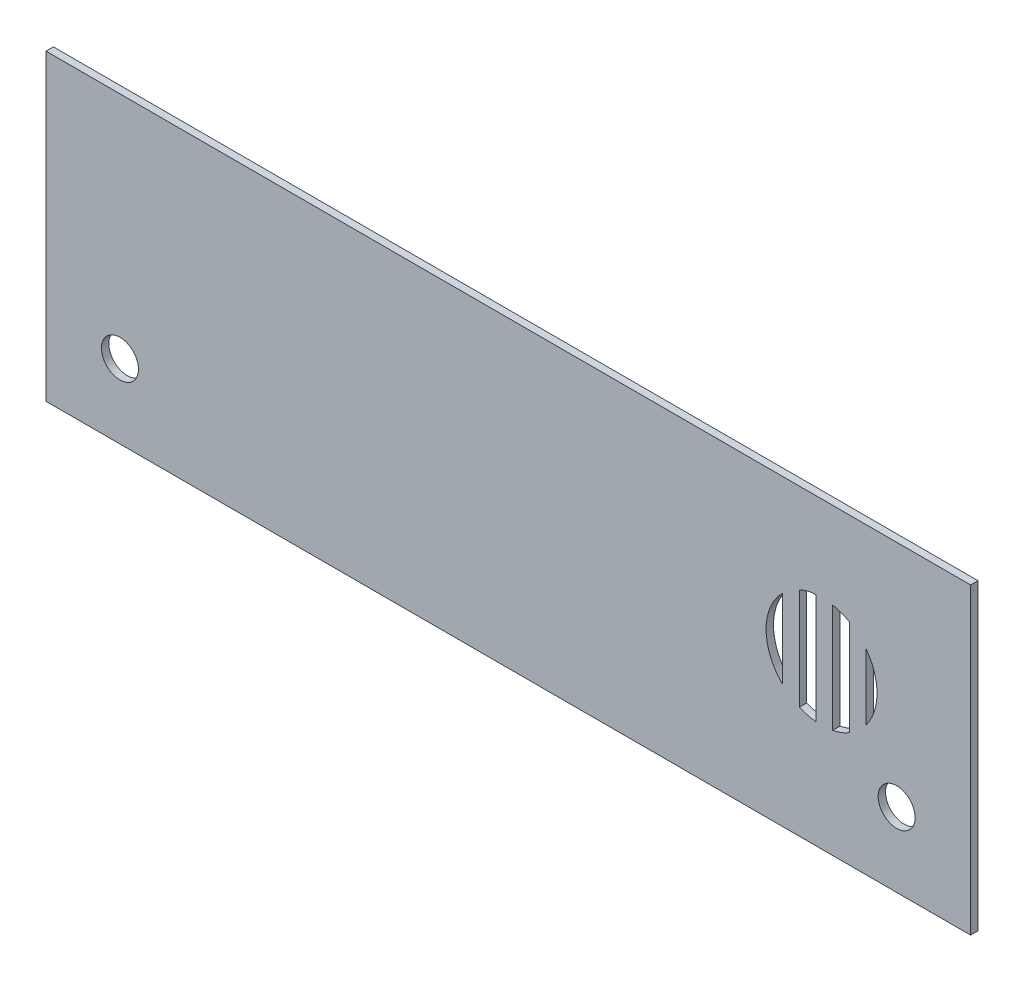
SolidWorks part; units mm, degrees
material "PC High Viscosity"
ref_plane "Front Plane" through (0, 0, 0) normal (0, 0, 1) x (1, 0, 0)
ref_plane "Top Plane" through (0, 0, 0) normal (0, 1, 0) x (1, 0, 0)
ref_plane "Right Plane" through (0, 0, 0) normal (1, 0, 0) x (0, 0, -1)
sketch "Sketch1" plane through (0, 0, 0) normal (0, 0, 1) x (1, 0, 0)
  line L1 (-125, 41) -> (125, 41)
  line L2 (-125, 41) -> (-125, -41)
  line L3 (-125, -41) -> (125, -41)
  line L4 (125, 41) -> (125, -41)
  line L5 (0, -41) -> (0, 41) construction
  line L6 (-125, 0) -> (125, 0) construction
  point P0 (0, 0)
  dimension "D1" = 250
  dimension "D2" = 82
extrude "Boss-Extrude1" add sketch "Sketch1" along normal blind 2
sketch "Sketch2" plane through (0, 0, 2) normal (0, 0, 1) x (1, 0, 0)
  line L0 (69.6958, 17.7737) -> (104.6997, 17.7737)
  line L1 (69.6958, -12.0162) -> (99.6958, -12.0162)
  line L2 (69.6958, 17.7737) -> (69.6958, -12.0162)
  line L3 (74.1958, 17.7737) -> (74.1958, -12.0162)
  line L4 (78.6958, 17.7737) -> (78.6958, -12.0162)
  line L5 (83.1958, 17.7737) -> (83.1958, -12.0162)
  line L6 (87.6958, 17.7737) -> (87.6958, -12.0162)
  line L7 (92.1958, 17.7737) -> (92.1958, -12.0162)
  line L8 (96.6958, 17.7737) -> (96.6958, -12.0162)
  circle A0 centre (84.6958, 2.9838) radius 15
  point P4 (87.7531, 17.6689)
  point P7 (84.6958, -12.0162)
  point P10 (87.1977, 17.7737)
  dimension "D1" = 30
extrude "Cut-Extrude1" cut sketch "Sketch2" against normal blind 3 contours L3 A0 | L0 A0 L4 L5 | L7 A0 L6 | L8 A0
sketch "Sketch3" plane through (0, 0, 2) normal (0, 0, 1) x (1, 0, 0)
  line L0 (-125, 41) -> (-125, -41) construction
  line L1 (125, -41) -> (125, 41) construction
  line L2 (-125, -41) -> (125, -41) construction
  circle A0 centre (-105, -21) radius 5
  circle A1 centre (105, -21) radius 5
  dimension "D1" = 20
  dimension "D5" = 10
  dimension "D2" = 20
  dimension "D3" = 20
  dimension "D4" = 20
extrude "Cut-Extrude2" cut sketch "Sketch3" against normal blind 3
